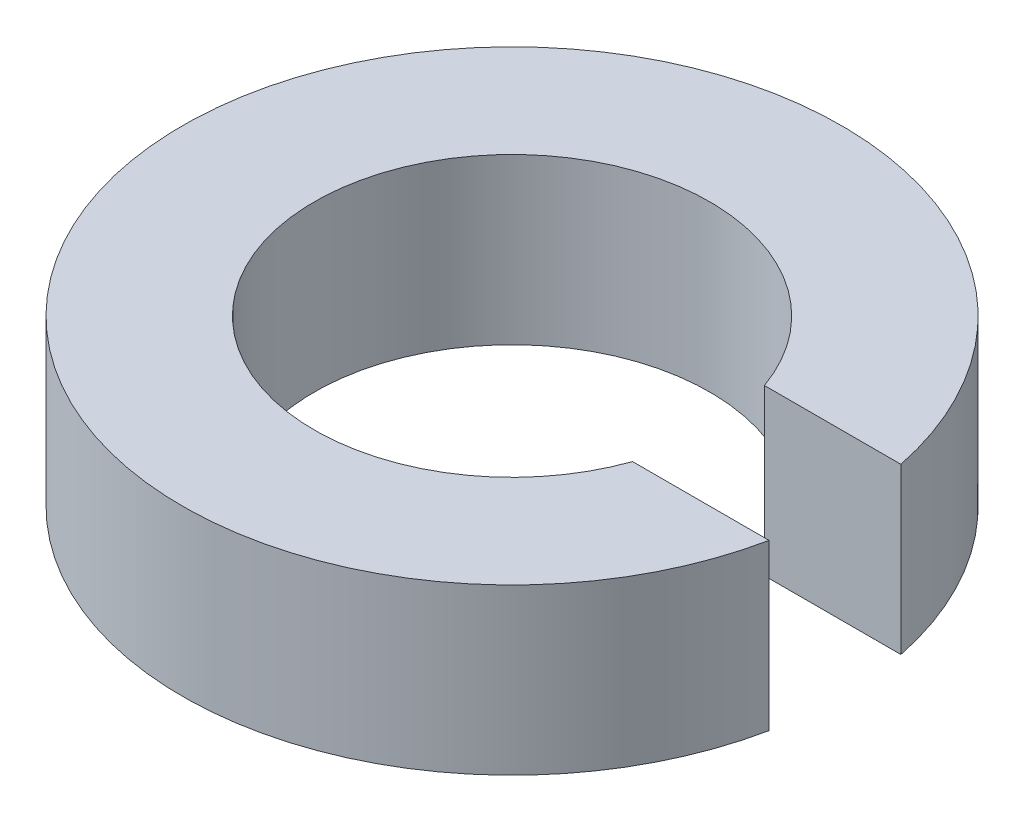
SolidWorks part; units mm, degrees
ref_plane "Front Plane" through (0, 0, 0) normal (0, 0, 1) x (1, 0, 0)
ref_plane "Top Plane" through (0, 0, 0) normal (0, 1, 0) x (1, 0, 0)
ref_plane "Right Plane" through (0, 0, 0) normal (1, 0, 0) x (0, 0, -1)
sketch "Sketch1" plane through (0, 0, 0) normal (0, 1, 0) x (1, 0, 0)
  line L0 (120, 20) -> (120, 0) construction
  line L1 (120, 20) -> (140, 20) construction
  line L2 (131.3137, 24) -> (139.5959, 24)
  line L3 (131.3137, 16) -> (139.5959, 16)
  arc A0 (139.5959, 24) -> (139.5959, 16) centre (120, 20) ccw
  arc A1 (131.3137, 24) -> (131.3137, 16) centre (120, 20) ccw
  dimension "D1" = 40
  dimension "D2" = 24
  dimension "D3" = 100
  dimension "D4" = 4
  dimension "D5" = 8
extrude "Boss-Extrude1" add sketch "Sketch1" along normal blind 10
